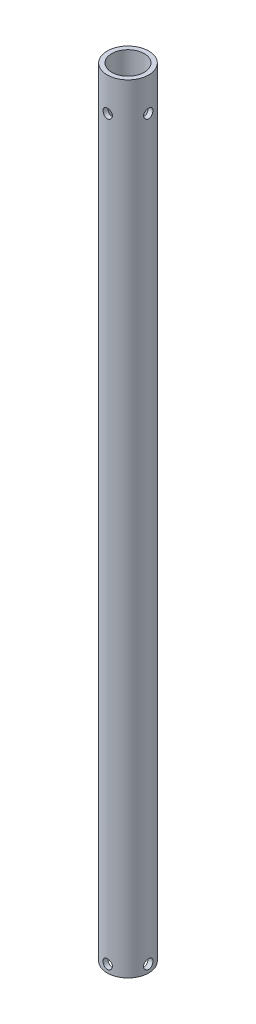
SolidWorks part; units mm, degrees
ref_plane "Front Plane" through (0, 0, 0) normal (0, 0, 1) x (1, 0, 0)
ref_plane "Top Plane" through (0, 0, 0) normal (0, 1, 0) x (1, 0, 0)
ref_plane "Right Plane" through (0, 0, 0) normal (1, 0, 0) x (0, 0, -1)
sketch "Sketch1" plane through (0, 0, 0) normal (0, 1, 0) x (1, 0, 0)
  circle A0 centre (0, 0) radius 10.45
  circle A1 centre (0, 0) radius 13.35
  dimension "D1" = 20.9
  dimension "D2" = 26.7
extrude "Boss-Extrude1" add sketch "Sketch1" along normal mid plane 500
sketch "Sketch2" plane through (0, 0, 0) normal (0, 0, 1) x (1, 0, 0)
  line L0 (10.45, 250) -> (-10.45, 250) construction
  line L1 (-13.35, -250) -> (13.35, -250) construction
  circle A0 centre (0, 228.58) radius 3
  circle A1 centre (0, -245) radius 3
  dimension "D2" = 6
  dimension "D1" = 21.42
  dimension "D3" = 5
extrude "Cut-Extrude1" cut sketch "Sketch2" along normal through all
pattern_circular "CirPattern1" count 2 over 90 about axis through (0, 250, 0) along (0, -1, 0) of "Cut-Extrude1"
